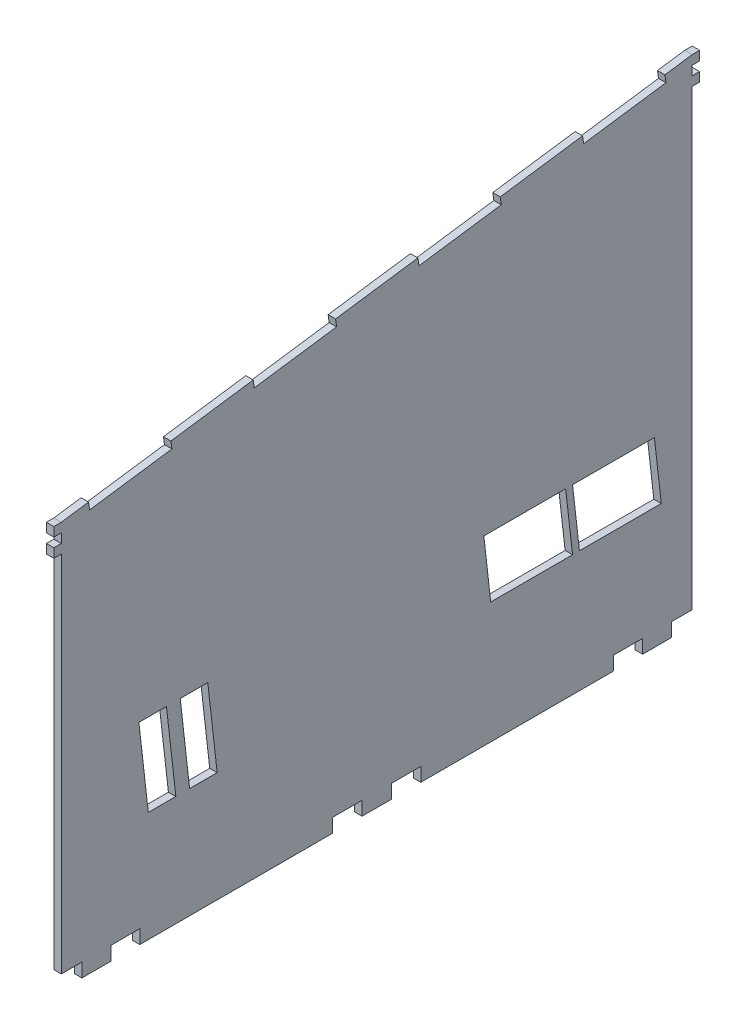
SolidWorks part; units mm, degrees
ref_plane "Ön Düzlem" through (0, 0, 0) normal (0, 0, 1) x (1, 0, 0)
ref_plane "Üst Düzlem" through (0, 0, 0) normal (0, 1, 0) x (1, 0, 0)
ref_plane "Sağ Düzlem" through (0, 0, 0) normal (1, 0, 0) x (0, 0, -1)
sketch "Sketch1" plane through (0, 0, 0) normal (1, 0, 0) x (0, 0, -1)
  line L20 (-107.0133, -114.8) -> (-96.5067, -114.8)
  line L34 (-96.5067, -109.8) -> (-86, -109.8)
  line L38 (-16, -109.8) -> (-5.3333, -109.8)
  line L39 (-5.3333, -114.8) -> (5.3333, -114.8)
  line L40 (-86, -114.8) -> (-16, -114.8)
  line L41 (5.3333, -109.8) -> (16, -109.8)
  line L48 (86, -109.8) -> (96.5067, -109.8)
  line L49 (96.5067, -114.8) -> (107.0133, -114.8)
  line L55 (107.0133, -109.8) -> (114.49, -109.8)
  line L84 (16, -114.8) -> (86, -114.8)
  line L209 (100.78, -48.8) -> (71.08, -48.8)
  line L211 (100.78, -70.8) -> (73.58, -70.8)
  line L212 (68.58, -48.8) -> (71.08, -70.8)
  line L215 (71.08, -48.8) -> (73.58, -70.8)
  line L216 (41.38, -48.8) -> (38.88, -48.8)
  line L217 (38.88, -48.8) -> (41.38, -70.8)
  line L218 (100.78, -70.8) -> (103.28, -70.8)
  line L219 (100.78, -48.8) -> (103.28, -70.8)
  line L220 (71.08, -70.8) -> (41.38, -70.8)
  line L221 (68.58, -48.8) -> (41.38, -48.8)
  line L226 (-72.9109, -74.8) -> (-76.32, -44.8)
  line L227 (-67.9109, -74.8) -> (-71.32, -44.8)
  line L233 (-82.9109, -74.8) -> (-86.32, -44.8)
  line L235 (-57.9109, -74.8) -> (-61.32, -44.8)
  line L238 (-62.9109, -74.8) -> (-66.32, -44.8) [skipped]
  line L239 (-76.32, -44.8) -> (-86.32, -44.8)
  line L240 (-82.9109, -74.8) -> (-72.9109, -74.8)
  line L241 (-67.9109, -74.8) -> (-57.9109, -74.8)
  line L242 (-71.32, -44.8) -> (-61.32, -44.8)
  line L273 (-114.5, -109.8) -> (-107.0133, -109.8)
  line L274 (114.49, -109.8) -> (114.5, -109.8)
  line L277 (107.0133, -114.8) -> (107.0133, -109.8)
  line L278 (96.5067, -114.8) -> (96.5067, -109.8)
  line L279 (86, -109.8) -> (86, -114.8)
  line L280 (16, -109.8) -> (16, -114.8)
  line L281 (-114.5, -109.8) -> (-114.5, 22.2)
  line L282 (-5.3333, -109.8) -> (-5.3333, -114.8)
  line L283 (5.3333, -109.8) -> (5.3333, -114.8)
  line L284 (-16, -109.8) -> (-16, -114.8)
  line L285 (-107.0133, -114.8) -> (-107.0133, -109.8)
  line L286 (-96.5067, -109.8) -> (-96.5067, -114.8)
  line L287 (-86, -114.8) -> (-86, -109.8)
  line L292 (-114.5, 32.2) -> (-104.5992, 33.6051)
  line L299 (114.49, -109.8) -> (114.5, 54.7)
  line L300 (-114.5, 28.8667) -> (-117.2, 28.8667)
  line L302 (-117.2, 28.8667) -> (-117.2, 32.2)
  line L303 (114.5, 58.0333) -> (117.2, 58.0333)
  line L304 (114.5, 61.3667) -> (117.2, 61.3667)
  line L305 (-114.5, 32.2) -> (-117.2, 32.2)
  line L306 (-117.2, 25.5333) -> (-117.2, 22.2)
  line L307 (-117.2, 22.2) -> (-114.5, 22.2)
  line L308 (-114.5, 25.5333) -> (-117.2, 25.5333)
  line L309 (-114.5, 28.8667) -> (-114.5, 25.5333)
  line L310 (114.5, 54.7) -> (117.2, 54.7)
  line L311 (117.2, 58.0333) -> (117.2, 54.7)
  line L312 (117.2, 61.3667) -> (117.2, 64.7)
  line L313 (117.2, 64.7) -> (114.5, 64.7)
  line L314 (114.5, 61.3667) -> (114.5, 58.0333)
  line L315 (114.5, 64.7) -> (104.5992, 63.2949)
  line L316 (-114.5, 32.2) -> (-104.5992, 33.6051)
  line L317 (104.5992, 63.2949) -> (114.5, 64.7)
  line L319 (104.5992, 63.2949) -> (104.9786, 60.6217)
  line L320 (104.9786, 60.6217) -> (75.0931, 56.3803)
  line L321 (-104.5992, 33.6051) -> (-104.2198, 30.9319)
  line L322 (74.7137, 59.0535) -> (44.8282, 54.8121)
  line L323 (45.2076, 52.1389) -> (15.3221, 47.8975)
  line L324 (14.9427, 50.5707) -> (-14.9427, 46.3293)
  line L325 (-14.5634, 43.6561) -> (-44.4488, 39.4147)
  line L326 (-44.8282, 42.0879) -> (-74.7137, 37.8465)
  line L327 (-74.3343, 35.1733) -> (-104.2198, 30.9319)
  line L328 (74.7137, 59.0535) -> (75.0931, 56.3803)
  line L329 (44.8282, 54.8121) -> (45.2076, 52.1389)
  line L330 (14.9427, 50.5707) -> (15.3221, 47.8975)
  line L331 (-14.9427, 46.3293) -> (-14.5634, 43.6561)
  line L332 (-44.8282, 42.0879) -> (-44.4488, 39.4147)
  line L333 (-74.7137, 37.8465) -> (-74.3343, 35.1733)
  point P0 (0, 0)
  dimension "D1" = 3
extrude "Boss-Extrude1" add sketch "Sketch1" along normal blind 2.7
